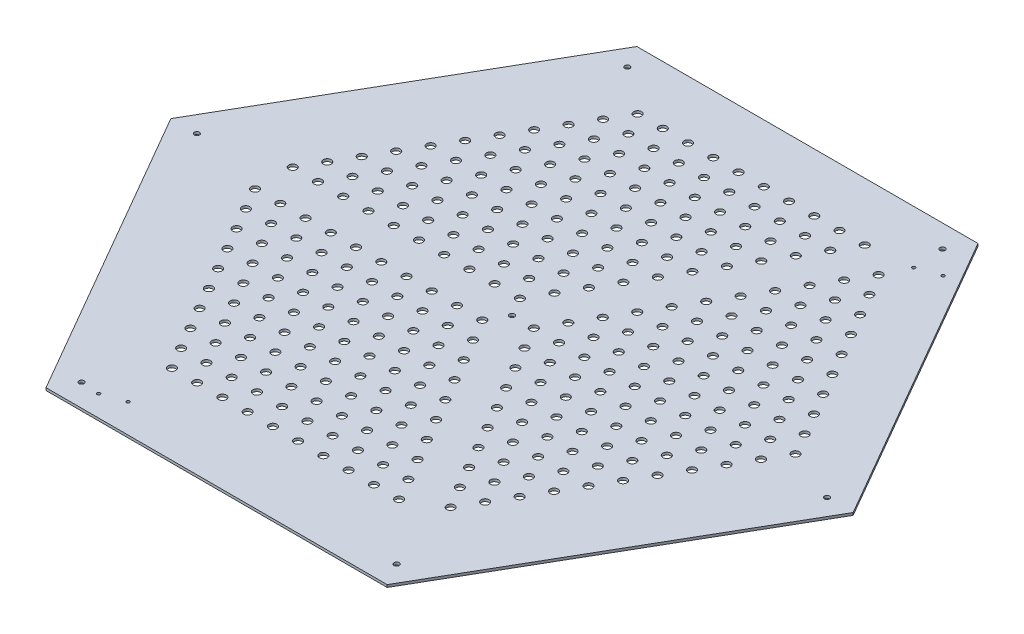
SolidWorks part; units mm, degrees
material "Pine"
ref_plane "Front Plane" through (0, 0, 0) normal (0, 0, 1) x (1, 0, 0)
ref_plane "Top Plane" through (0, 0, 0) normal (0, 1, 0) x (1, 0, 0)
ref_plane "Right Plane" through (0, 0, 0) normal (1, 0, 0) x (0, 0, -1)
sketch "Sketch1" plane through (0, 0, 0) normal (0, 1, 0) x (1, 0, 0)
  line L1 (433.0127, 0) -> (216.5064, 375)
  line L2 (216.5064, 375) -> (-216.5064, 375)
  line L3 (-216.5064, 375) -> (-433.0127, 0)
  line L4 (-433.0127, 0) -> (-216.5064, -375)
  line L5 (-216.5064, -375) -> (216.5064, -375)
  line L6 (216.5064, -375) -> (433.0127, 0)
  circle A1 centre (0, 0) radius 375 construction
extrude "Base" add sketch "Sketch1" along normal blind 3.175
sketch "Border Sketch" plane through (0, 3.175, 0) normal (0, 1, 0) x (1, 0, 0)
  line L7 (450, 0) -> (225, 389.7114)
  line L8 (225, 389.7114) -> (-225, 389.7114)
  line L9 (-225, 389.7114) -> (-450, 0)
  line L10 (-450, 0) -> (-225, -389.7114)
  line L11 (-225, -389.7114) -> (225, -389.7114)
  line L12 (225, -389.7114) -> (450, 0)
  line L14 (225, 389.7114) -> (0, 0)
  line L15 (0, 0) -> (225, -389.7114)
  line L20 (-450, 0) -> (0, 0)
  line L21 (0, 5.5) -> (-446.8246, 5.5)
  line L22 (0, -5.5) -> (-446.8246, -5.5)
  line L23 (218.6491, 389.7114) -> (-4.7631, 2.75)
  line L24 (4.7631, -2.75) -> (228.1754, 384.2114)
  line L25 (4.7631, 2.75) -> (228.1754, -384.2114)
  line L26 (-4.7631, -2.75) -> (218.6491, -389.7114)
  circle A0 centre (0, 0) radius 450 construction
  circle A1 centre (0, 0) radius 5.5
  dimension "D1" = 5.5
  dimension "D2" = 5.5
  dimension "D3" = 5.5
  dimension "D4" = 5.5
sketch "Sketch3" plane through (0, 3.175, 0) normal (0, 1, 0) x (1, 0, 0)
  circle A1 centre (27.6379, 0.0432) radius 5
  circle A2 centre (43.6579, 27.7907) radius 5
  circle A3 centre (59.6779, 55.5381) radius 5
  circle A4 centre (75.6979, 83.2856) radius 5
  circle A5 centre (91.7179, 111.0331) radius 5
  circle A6 centre (107.7379, 138.7805) radius 5
  circle A7 centre (123.7579, 166.528) radius 5
  circle A8 centre (139.7779, 194.2754) radius 5
  circle A9 centre (155.7979, 222.0229) radius 5
  circle A10 centre (171.8179, 249.7703) radius 5
  circle A11 centre (187.8379, 277.5178) radius 5
  circle A12 centre (59.6779, 0.0432) radius 5
  circle A13 centre (75.6979, 27.7907) radius 5
  circle A14 centre (91.7179, 55.5381) radius 5
  circle A15 centre (107.7379, 83.2856) radius 5
  circle A16 centre (123.7579, 111.0331) radius 5
  circle A17 centre (139.7779, 138.7805) radius 5
  circle A18 centre (155.7979, 166.528) radius 5
  circle A19 centre (171.8179, 194.2754) radius 5
  circle A20 centre (187.8379, 222.0229) radius 5
  circle A21 centre (203.8579, 249.7703) radius 5
  circle A22 centre (75.6979, -27.7042) radius 5
  circle A23 centre (91.7179, 0.0432) radius 5
  circle A24 centre (107.7379, 27.7907) radius 5
  circle A25 centre (123.7579, 55.5381) radius 5
  circle A26 centre (139.7779, 83.2856) radius 5
  circle A27 centre (155.7979, 111.0331) radius 5
  circle A28 centre (171.8179, 138.7805) radius 5
  circle A29 centre (187.8379, 166.528) radius 5
  circle A30 centre (203.8579, 194.2754) radius 5
  circle A31 centre (219.8779, 222.0229) radius 5
  circle A32 centre (91.7179, -55.4517) radius 5
  circle A33 centre (107.7379, -27.7042) radius 5
  circle A34 centre (123.7579, 0.0432) radius 5
  circle A35 centre (139.7779, 27.7907) radius 5
  circle A36 centre (155.7979, 55.5381) radius 5
  circle A37 centre (171.8179, 83.2856) radius 5
  circle A38 centre (187.8379, 111.0331) radius 5
  circle A39 centre (203.8579, 138.7805) radius 5
  circle A40 centre (219.8779, 166.528) radius 5
  circle A41 centre (235.8979, 194.2754) radius 5
  circle A42 centre (107.7379, -83.1991) radius 5
  circle A43 centre (123.7579, -55.4517) radius 5
  circle A44 centre (139.7779, -27.7042) radius 5
  circle A45 centre (155.7979, 0.0432) radius 5
  circle A46 centre (171.8179, 27.7907) radius 5
  circle A47 centre (187.8379, 55.5381) radius 5
  circle A48 centre (203.8579, 83.2856) radius 5
  circle A49 centre (219.8779, 111.0331) radius 5
  circle A50 centre (235.8979, 138.7805) radius 5
  circle A51 centre (251.9179, 166.528) radius 5
  circle A52 centre (123.7579, -110.9466) radius 5
  circle A53 centre (139.7779, -83.1991) radius 5
  circle A54 centre (155.7979, -55.4517) radius 5
  circle A55 centre (171.8179, -27.7042) radius 5
  circle A56 centre (187.8379, 0.0432) radius 5
  circle A57 centre (203.8579, 27.7907) radius 5
  circle A58 centre (219.8779, 55.5381) radius 5
  circle A59 centre (235.8979, 83.2856) radius 5
  circle A60 centre (251.9179, 111.0331) radius 5
  circle A61 centre (267.9379, 138.7805) radius 5
  circle A62 centre (139.7779, -138.694) radius 5
  circle A63 centre (155.7979, -110.9466) radius 5
  circle A64 centre (171.8179, -83.1991) radius 5
  circle A65 centre (187.8379, -55.4517) radius 5
  circle A66 centre (203.8579, -27.7042) radius 5
  circle A67 centre (219.8779, 0.0432) radius 5
  circle A68 centre (235.8979, 27.7907) radius 5
  circle A69 centre (251.9179, 55.5381) radius 5
  circle A70 centre (267.9379, 83.2856) radius 5
  circle A71 centre (283.9579, 111.0331) radius 5
  circle A72 centre (155.7979, -166.4415) radius 5
  circle A73 centre (171.8179, -138.694) radius 5
  circle A74 centre (187.8379, -110.9466) radius 5
  circle A75 centre (203.8579, -83.1991) radius 5
  circle A76 centre (219.8779, -55.4517) radius 5
  circle A77 centre (235.8979, -27.7042) radius 5
  circle A78 centre (251.9179, 0.0432) radius 5
  circle A79 centre (267.9379, 27.7907) radius 5
  circle A80 centre (283.9579, 55.5381) radius 5
  circle A81 centre (299.9779, 83.2856) radius 5
  circle A82 centre (171.8179, -194.1889) radius 5
  circle A83 centre (187.8379, -166.4415) radius 5
  circle A84 centre (203.8579, -138.694) radius 5
  circle A85 centre (219.8779, -110.9466) radius 5
  circle A86 centre (235.8979, -83.1991) radius 5
  circle A87 centre (251.9179, -55.4517) radius 5
  circle A88 centre (267.9379, -27.7042) radius 5
  circle A89 centre (283.9579, 0.0432) radius 5
  circle A90 centre (299.9779, 27.7907) radius 5
  circle A91 centre (315.9979, 55.5381) radius 5
  circle A92 centre (187.8379, -221.9364) radius 5
  circle A93 centre (203.8579, -194.1889) radius 5
  circle A94 centre (219.8779, -166.4415) radius 5
  circle A95 centre (235.8979, -138.694) radius 5
  circle A96 centre (251.9179, -110.9466) radius 5
  circle A97 centre (267.9379, -83.1991) radius 5
  circle A98 centre (283.9579, -55.4517) radius 5
  circle A99 centre (299.9779, -27.7042) radius 5
  circle A100 centre (315.9979, 0.0432) radius 5
  circle A101 centre (332.0179, 27.7907) radius 5
  circle A102 centre (43.6579, -27.7042) radius 5
  circle A103 centre (59.6779, -55.4517) radius 5
  circle A104 centre (75.6979, -83.1991) radius 5
  circle A105 centre (91.7179, -110.9466) radius 5
  circle A106 centre (107.7379, -138.694) radius 5
  circle A107 centre (123.7579, -166.4415) radius 5
  circle A108 centre (139.7779, -194.1889) radius 5
  circle A109 centre (155.7979, -221.9364) radius 5
  circle A110 centre (171.8179, -249.6838) radius 5
  circle A111 centre (-13.8564, -23.9135) radius 5
  circle A112 centre (-45.8964, -23.9135) radius 5
  circle A113 centre (-77.9364, -23.9135) radius 5
  circle A114 centre (-109.9764, -23.9135) radius 5
  circle A115 centre (-142.0164, -23.9135) radius 5
  circle A116 centre (-174.0564, -23.9135) radius 5
  circle A117 centre (-206.0964, -23.9135) radius 5
  circle A118 centre (-238.1364, -23.9135) radius 5
  circle A119 centre (-270.1764, -23.9135) radius 5
  circle A120 centre (-302.2164, -23.9135) radius 5
  circle A121 centre (-29.8764, -51.661) radius 5
  circle A122 centre (-61.9164, -51.661) radius 5
  circle A123 centre (-93.9564, -51.661) radius 5
  circle A124 centre (-125.9964, -51.661) radius 5
  circle A125 centre (-158.0364, -51.661) radius 5
  circle A126 centre (-190.0764, -51.661) radius 5
  circle A127 centre (-222.1164, -51.661) radius 5
  circle A128 centre (-254.1564, -51.661) radius 5
  circle A129 centre (-286.1964, -51.661) radius 5
  circle A130 centre (-13.8564, -79.4084) radius 5
  circle A131 centre (-45.8964, -79.4084) radius 5
  circle A132 centre (-77.9364, -79.4084) radius 5
  circle A133 centre (-109.9764, -79.4084) radius 5
  circle A134 centre (-142.0164, -79.4084) radius 5
  circle A135 centre (-174.0564, -79.4084) radius 5
  circle A136 centre (-206.0964, -79.4084) radius 5
  circle A137 centre (-238.1364, -79.4084) radius 5
  circle A138 centre (-270.1764, -79.4084) radius 5
  circle A139 centre (2.1636, -107.1559) radius 5
  circle A140 centre (-29.8764, -107.1559) radius 5
  circle A141 centre (-61.9164, -107.1559) radius 5
  circle A142 centre (-93.9564, -107.1559) radius 5
  circle A143 centre (-125.9964, -107.1559) radius 5
  circle A144 centre (-158.0364, -107.1559) radius 5
  circle A145 centre (-190.0764, -107.1559) radius 5
  circle A146 centre (-222.1164, -107.1559) radius 5
  circle A147 centre (-254.1564, -107.1559) radius 5
  circle A148 centre (18.1836, -134.9033) radius 5
  circle A149 centre (-13.8564, -134.9033) radius 5
  circle A150 centre (-45.8964, -134.9033) radius 5
  circle A151 centre (-77.9364, -134.9033) radius 5
  circle A152 centre (-109.9764, -134.9033) radius 5
  circle A153 centre (-142.0164, -134.9033) radius 5
  circle A154 centre (-174.0564, -134.9033) radius 5
  circle A155 centre (-206.0964, -134.9033) radius 5
  circle A156 centre (-238.1364, -134.9033) radius 5
  circle A157 centre (34.2036, -162.6508) radius 5
  circle A158 centre (2.1636, -162.6508) radius 5
  circle A159 centre (-29.8764, -162.6508) radius 5
  circle A160 centre (-61.9164, -162.6508) radius 5
  circle A161 centre (-93.9564, -162.6508) radius 5
  circle A162 centre (-125.9964, -162.6508) radius 5
  circle A163 centre (-158.0364, -162.6508) radius 5
  circle A164 centre (-190.0764, -162.6508) radius 5
  circle A165 centre (-222.1164, -162.6508) radius 5
  circle A166 centre (50.2236, -190.3982) radius 5
  circle A167 centre (18.1836, -190.3982) radius 5
  circle A168 centre (-13.8564, -190.3982) radius 5
  circle A169 centre (-45.8964, -190.3982) radius 5
  circle A170 centre (-77.9364, -190.3982) radius 5
  circle A171 centre (-109.9764, -190.3982) radius 5
  circle A172 centre (-142.0164, -190.3982) radius 5
  circle A173 centre (-174.0564, -190.3982) radius 5
  circle A174 centre (-206.0964, -190.3982) radius 5
  circle A175 centre (66.2436, -218.1457) radius 5
  circle A176 centre (34.2036, -218.1457) radius 5
  circle A177 centre (2.1636, -218.1457) radius 5
  circle A178 centre (-29.8764, -218.1457) radius 5
  circle A179 centre (-61.9164, -218.1457) radius 5
  circle A180 centre (-93.9564, -218.1457) radius 5
  circle A181 centre (-125.9964, -218.1457) radius 5
  circle A182 centre (-158.0364, -218.1457) radius 5
  circle A183 centre (-190.0764, -218.1457) radius 5
  circle A184 centre (82.2636, -245.8932) radius 5
  circle A185 centre (50.2236, -245.8932) radius 5
  circle A186 centre (18.1836, -245.8932) radius 5
  circle A187 centre (-13.8564, -245.8932) radius 5
  circle A188 centre (-45.8964, -245.8932) radius 5
  circle A189 centre (-77.9364, -245.8932) radius 5
  circle A190 centre (-109.9764, -245.8932) radius 5
  circle A191 centre (-142.0164, -245.8932) radius 5
  circle A192 centre (-174.0564, -245.8932) radius 5
  circle A193 centre (98.2836, -273.6406) radius 5
  circle A194 centre (66.2436, -273.6406) radius 5
  circle A195 centre (34.2036, -273.6406) radius 5
  circle A196 centre (2.1636, -273.6406) radius 5
  circle A197 centre (-29.8764, -273.6406) radius 5
  circle A198 centre (-61.9164, -273.6406) radius 5
  circle A199 centre (-93.9564, -273.6406) radius 5
  circle A200 centre (-125.9964, -273.6406) radius 5
  circle A201 centre (-158.0364, -273.6406) radius 5
  circle A202 centre (2.1636, -51.661) radius 5
  circle A203 centre (18.1836, -79.4084) radius 5
  circle A204 centre (34.2036, -107.1559) radius 5
  circle A205 centre (50.2236, -134.9033) radius 5
  circle A206 centre (66.2436, -162.6508) radius 5
  circle A207 centre (82.2636, -190.3982) radius 5
  circle A208 centre (98.2836, -218.1457) radius 5
  circle A209 centre (114.3036, -245.8932) radius 5
  circle A210 centre (130.3236, -273.6406) radius 5
  circle A211 centre (-13.8564, 23.9135) radius 5
  circle A212 centre (2.1636, 51.661) radius 5
  circle A213 centre (18.1836, 79.4084) radius 5
  circle A214 centre (34.2036, 107.1559) radius 5
  circle A215 centre (50.2236, 134.9033) radius 5
  circle A216 centre (66.2436, 162.6508) radius 5
  circle A217 centre (82.2636, 190.3982) radius 5
  circle A218 centre (98.2836, 218.1457) radius 5
  circle A219 centre (114.3036, 245.8932) radius 5
  circle A220 centre (130.3236, 273.6406) radius 5
  circle A221 centre (146.3436, 301.3881) radius 5
  circle A222 centre (-29.8764, 51.661) radius 5
  circle A223 centre (-13.8564, 79.4084) radius 5
  circle A224 centre (2.1636, 107.1559) radius 5
  circle A225 centre (18.1836, 134.9033) radius 5
  circle A226 centre (34.2036, 162.6508) radius 5
  circle A227 centre (50.2236, 190.3982) radius 5
  circle A228 centre (66.2436, 218.1457) radius 5
  circle A229 centre (82.2636, 245.8932) radius 5
  circle A230 centre (98.2836, 273.6406) radius 5
  circle A231 centre (114.3036, 301.3881) radius 5
  circle A232 centre (-61.9164, 51.661) radius 5
  circle A233 centre (-45.8964, 79.4084) radius 5
  circle A234 centre (-29.8764, 107.1559) radius 5
  circle A235 centre (-13.8564, 134.9033) radius 5
  circle A236 centre (2.1636, 162.6508) radius 5
  circle A237 centre (18.1836, 190.3982) radius 5
  circle A238 centre (34.2036, 218.1457) radius 5
  circle A239 centre (50.2236, 245.8932) radius 5
  circle A240 centre (66.2436, 273.6406) radius 5
  circle A241 centre (82.2636, 301.3881) radius 5
  circle A242 centre (-93.9564, 51.661) radius 5
  circle A243 centre (-77.9364, 79.4084) radius 5
  circle A244 centre (-61.9164, 107.1559) radius 5
  circle A245 centre (-45.8964, 134.9033) radius 5
  circle A246 centre (-29.8764, 162.6508) radius 5
  circle A247 centre (-13.8564, 190.3982) radius 5
  circle A248 centre (2.1636, 218.1457) radius 5
  circle A249 centre (18.1836, 245.8932) radius 5
  circle A250 centre (34.2036, 273.6406) radius 5
  circle A251 centre (50.2236, 301.3881) radius 5
  circle A252 centre (-125.9964, 51.661) radius 5
  circle A253 centre (-109.9764, 79.4084) radius 5
  circle A254 centre (-93.9564, 107.1559) radius 5
  circle A255 centre (-77.9364, 134.9033) radius 5
  circle A256 centre (-61.9164, 162.6508) radius 5
  circle A257 centre (-45.8964, 190.3982) radius 5
  circle A258 centre (-29.8764, 218.1457) radius 5
  circle A259 centre (-13.8564, 245.8932) radius 5
  circle A260 centre (2.1636, 273.6406) radius 5
  circle A261 centre (18.1836, 301.3881) radius 5
  circle A262 centre (-158.0364, 51.661) radius 5
  circle A263 centre (-142.0164, 79.4084) radius 5
  circle A264 centre (-125.9964, 107.1559) radius 5
  circle A265 centre (-109.9764, 134.9033) radius 5
  circle A266 centre (-93.9564, 162.6508) radius 5
  circle A267 centre (-77.9364, 190.3982) radius 5
  circle A268 centre (-61.9164, 218.1457) radius 5
  circle A269 centre (-45.8964, 245.8932) radius 5
  circle A270 centre (-29.8764, 273.6406) radius 5
  circle A271 centre (-13.8564, 301.3881) radius 5
  circle A272 centre (-190.0764, 51.661) radius 5
  circle A273 centre (-174.0564, 79.4084) radius 5
  circle A274 centre (-158.0364, 107.1559) radius 5
  circle A275 centre (-142.0164, 134.9033) radius 5
  circle A276 centre (-125.9964, 162.6508) radius 5
  circle A277 centre (-109.9764, 190.3982) radius 5
  circle A278 centre (-93.9564, 218.1457) radius 5
  circle A279 centre (-77.9364, 245.8932) radius 5
  circle A280 centre (-61.9164, 273.6406) radius 5
  circle A281 centre (-45.8964, 301.3881) radius 5
  circle A282 centre (-222.1164, 51.661) radius 5
  circle A283 centre (-206.0964, 79.4084) radius 5
  circle A284 centre (-190.0764, 107.1559) radius 5
  circle A285 centre (-174.0564, 134.9033) radius 5
  circle A286 centre (-158.0364, 162.6508) radius 5
  circle A287 centre (-142.0164, 190.3982) radius 5
  circle A288 centre (-125.9964, 218.1457) radius 5
  circle A289 centre (-109.9764, 245.8932) radius 5
  circle A290 centre (-93.9564, 273.6406) radius 5
  circle A291 centre (-77.9364, 301.3881) radius 5
  circle A292 centre (-254.1564, 51.661) radius 5
  circle A293 centre (-238.1364, 79.4084) radius 5
  circle A294 centre (-222.1164, 107.1559) radius 5
  circle A295 centre (-206.0964, 134.9033) radius 5
  circle A296 centre (-190.0764, 162.6508) radius 5
  circle A297 centre (-174.0564, 190.3982) radius 5
  circle A298 centre (-158.0364, 218.1457) radius 5
  circle A299 centre (-142.0164, 245.8932) radius 5
  circle A300 centre (-125.9964, 273.6406) radius 5
  circle A301 centre (-109.9764, 301.3881) radius 5
  circle A302 centre (-286.1964, 51.661) radius 5
  circle A303 centre (-270.1764, 79.4084) radius 5
  circle A304 centre (-254.1564, 107.1559) radius 5
  circle A305 centre (-238.1364, 134.9033) radius 5
  circle A306 centre (-222.1164, 162.6508) radius 5
  circle A307 centre (-206.0964, 190.3982) radius 5
  circle A308 centre (-190.0764, 218.1457) radius 5
  circle A309 centre (-174.0564, 245.8932) radius 5
  circle A310 centre (-158.0364, 273.6406) radius 5
  circle A311 centre (-142.0164, 301.3881) radius 5
  circle A312 centre (-45.8964, 23.9135) radius 5
  circle A313 centre (-77.9364, 23.9135) radius 5
  circle A314 centre (-109.9764, 23.9135) radius 5
  circle A315 centre (-142.0164, 23.9135) radius 5
  circle A316 centre (-174.0564, 23.9135) radius 5
  circle A317 centre (-206.0964, 23.9135) radius 5
  circle A318 centre (-238.1364, 23.9135) radius 5
  circle A319 centre (-270.1764, 23.9135) radius 5
  circle A320 centre (-302.2164, 23.9135) radius 5
  dimension "D1" = 11
  dimension "D3" = 10
  dimension "D5" = 11
  dimension "D2" = 10
  dimension "D4" = 10
  dimension "D6" = 10
extrude "Cut-Extrude1" cut sketch "Sketch3" against normal up to next (3.175 mm away)
hole_wizard "Ø6.5 (6.5) Diameter Hole1" positions "Sketch4" profile "Sketch5" hole size "Ø6.5" standard "ANSI Metric"
sketch "Sketch4" plane through (0, -4.7625, 0) normal (0, -1, 0) x (-0.5, 0, 0.866)
  point P0 (0, 0)
  point P3 (-400, 0)
  point P11 (-200, 346.4102)
  point P12 (200, 346.4102)
  point P13 (400, 0)
  point P14 (200, -346.4102)
  point P15 (-200, -346.4102)
  point P16 (0, 0)
sketch "Sketch5" plane through (0, -4.7625, 0) normal (1, 0, 0) x (0, 0, -1)
  line L0 (0, 0) -> (0, 7.9375)
  line L1 (0, 7.9375) -> (3.25, 7.9375)
  line L2 (3.25, 7.9375) -> (3.25, 0)
  line L3 (3.25, 0) -> (0, 0)
  line L4 (0, -6.35) -> (0, 107.95) construction
  dimension "Thru Hole Dia." = 6.5
  dimension "Thru Hole Depth" = 7.9375
hole_wizard "Ø4.0 (4) Diameter Hole1" positions "Sketch6" profile "Sketch7" hole size "Ø4.0" standard "ANSI Metric"
sketch "Sketch6" plane through (0, 9.525, 0) normal (0, 1, 0) x (0.5, 0, -0.866)
  point P0 (-389.7627, -21.2724)
  point P3 (-367.5377, -40.3224)
  point P6 (367.5377, -21.2724)
  point P9 (389.7627, -40.3224)
sketch "Sketch7" plane through (-176.4589, 9.525, 348.1806) normal (1, 0, 0) x (0, 0, 1)
  line L0 (0, 0) -> (0, 9.525)
  line L1 (0, 9.525) -> (2, 9.525)
  line L2 (2, 9.525) -> (2, 0)
  line L3 (2, 0) -> (0, 0)
  line L4 (0, -6.35) -> (0, 107.95) construction
  dimension "Thru Hole Dia." = 4
  dimension "Thru Hole Depth" = 9.525
